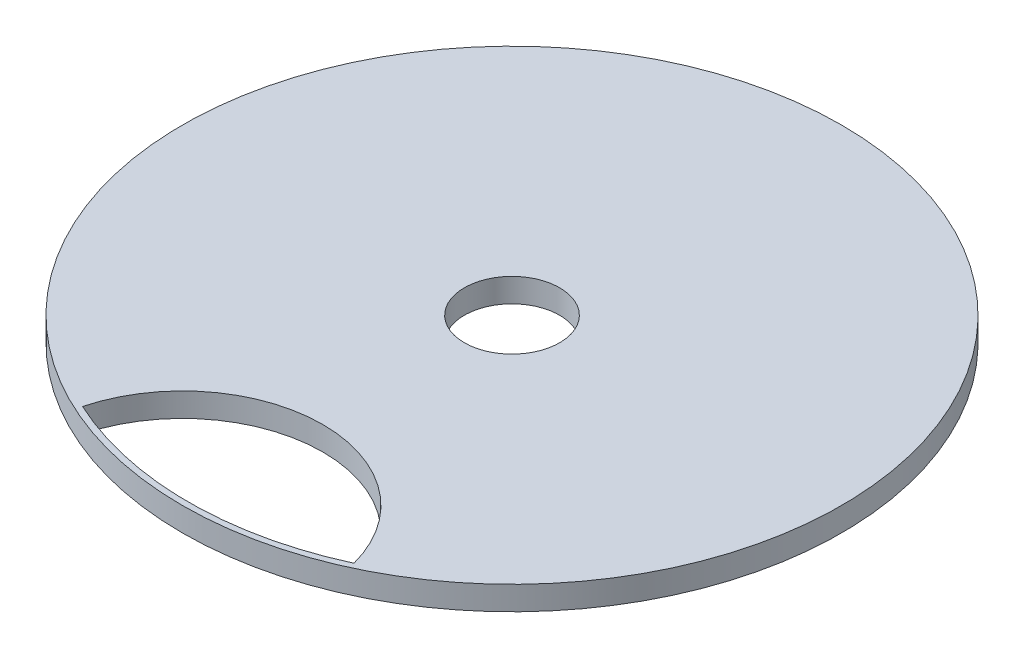
SolidWorks part; units mm, degrees
ref_plane "Front Plane" through (0, 0, 0) normal (0, 0, 1) x (1, 0, 0)
ref_plane "Top Plane" through (0, 0, 0) normal (0, 1, 0) x (1, 0, 0)
ref_plane "Right Plane" through (0, 0, 0) normal (1, 0, 0) x (0, 0, -1)
sketch "Sketch1" plane through (0, 0, 0) normal (0, 1, 0) x (1, 0, 0)
  line L0 (-110.8954, 0) -> (157.1018, 0) construction
  line L1 (0, 99.4797) -> (0, -86.9768) construction
  circle A0 centre (0, 0) radius 41.5
  circle A1 centre (0, 0) radius 6
  dimension "D1" = 83
  dimension "D2" = 12
extrude "Boss-Extrude1" add sketch "Sketch1" along normal blind 3
ref_plane "Plane1" through (0, 3, 0) normal (0, 1, 0) x (1, 0, 0)
sketch "Sketch2" plane through (0, 3, 0) normal (0, 1, 0) x (1, 0, 0)
  line L0 (-62.7867, 0) -> (66.48, 0) construction
  line L1 (0, 46.9054) -> (0, -49.4907) construction
  line L2 (-17.0918, -36.9923) -> (-17.4768, -42.5719)
  line L3 (-17.4768, -42.5719) -> (17.0918, -42.5719)
  line L4 (17.0918, -42.5719) -> (17.0918, -36.9923)
  arc A0 (17.0918, -36.9923) -> (-17.0918, -36.9923) centre (0, -41.5) ccw
  circle A1 centre (0, 0) radius 41.5 construction
  arc A2 (0, -40.75) -> (-17.0918, -36.9923) centre (0, 0) ccw
  arc A3 (-17.0918, -36.9923) -> (17.0918, -36.9923) centre (0, 0) ccw
  dimension "D1" = 81.5
extrude "Cut-Extrude1" cut sketch "Sketch2" against normal blind 3 contours A0 A2
sketch "Sketch3" plane through (0, 3, 0) normal (0, 1, 0) x (1, 0, 0)
  circle A0 centre (0, 0) radius 6
  dimension "D1" = 12
ref_plane "Plane2" through (0, 3, 0) normal (0, 1, 0) x (1, 0, 0)
sketch "Sketch4" plane through (0, 3, 0) normal (0, 1, 0) x (1, 0, 0)
  circle A0 centre (0, 0) radius 6
  circle A1 centre (0, 0) radius 10
  dimension "D1" = 20
